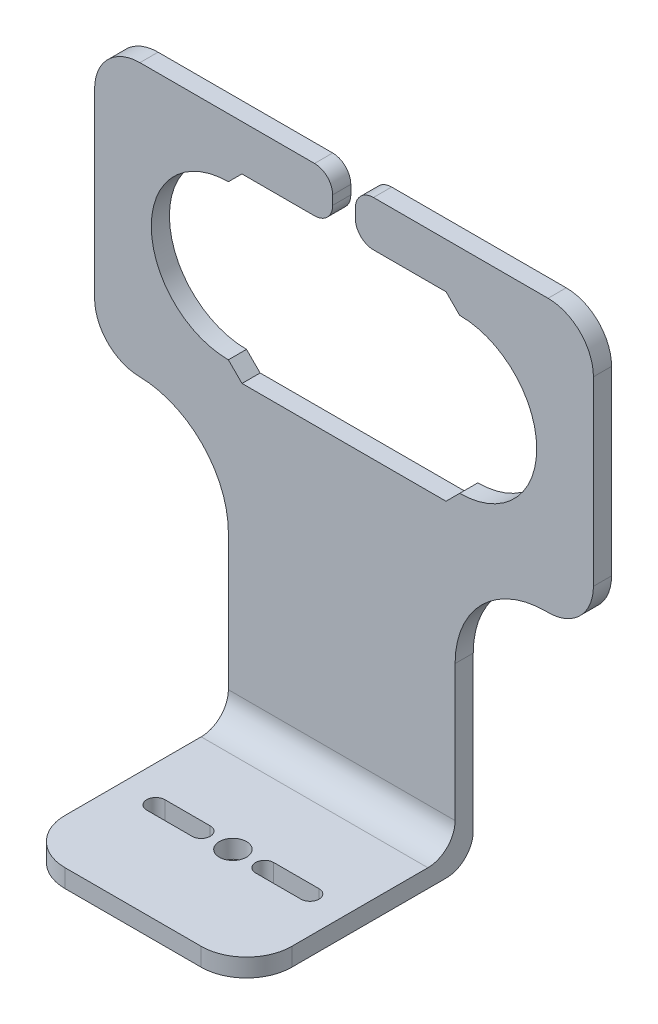
SolidWorks part; units mm, degrees
material "ABS"
ref_plane "Front Plane" through (0, 0, 0) normal (0, 0, 1) x (1, 0, 0)
ref_plane "Top Plane" through (0, 0, 0) normal (0, 1, 0) x (1, 0, 0)
ref_plane "Right Plane" through (0, 0, 0) normal (1, 0, 0) x (0, 0, -1)
sketch "Sketch1" plane through (0, 0, 0) normal (0, 0, 1) x (1, 0, 0)
  line L0 (-1.3335, 27.9084) -> (-1.3335, 26.9043)
  line L1 (-22.5835, 29.9084) -> (-3.3335, 29.9084)
  line L2 (-27.5835, 24.9084) -> (-27.5835, 4.9043)
  line L4 (27.4165, 24.9084) -> (27.4165, 4.9043)
  line L5 (-11.3376, 24.9043) -> (-3.3335, 24.9043)
  line L7 (-12.8335, -30.0916) -> (-12.8335, -0.0957)
  line L8 (12.1665, -30.0916) -> (12.1665, -0.0957)
  line L9 (-22.5835, -0.0957) -> (-12.8335, -0.0957)
  line L11 (12.1665, -0.0957) -> (22.4165, -0.0957)
  line L14 (-11.3294, 4.9043) -> (11.1624, 4.9043)
  line L16 (-12.8335, 23.4084) -> (-11.3376, 24.9043)
  line L17 (12.6665, 23.4084) -> (11.1706, 24.9043)
  line L18 (1.1665, 27.9084) -> (1.1665, 26.9043)
  line L19 (-12.8335, 6.4084) -> (-11.3294, 4.9043)
  line L20 (12.6665, 6.4084) -> (11.1624, 4.9043)
  line L21 (3.1665, 24.9043) -> (11.1706, 24.9043)
  line L22 (3.1665, 29.9084) -> (22.4165, 29.9084)
  line L23 (12.1665, -30.0916) -> (-12.8335, -30.0916)
  arc A0 (-12.8335, 23.4084) -> (-12.8335, 6.4084) centre (-12.8335, 14.9084) ccw
  arc A1 (12.6665, 6.4084) -> (12.6665, 23.4084) centre (12.6665, 14.9084) ccw
  arc A2 (22.4165, 29.9084) -> (27.4165, 24.9084) centre (22.4165, 24.9084) cw
  arc A3 (27.4165, 4.9043) -> (22.4165, -0.0957) centre (22.4165, 4.9043) cw
  arc A4 (-22.5835, -0.0957) -> (-27.5835, 4.9043) centre (-22.5835, 4.9043) cw
  arc A5 (-22.5835, 29.9084) -> (-27.5835, 24.9084) centre (-22.5835, 24.9084) ccw
  arc A6 (1.1665, 26.9043) -> (3.1665, 24.9043) centre (3.1665, 26.9043) ccw
  arc A7 (3.1665, 29.9084) -> (1.1665, 27.9084) centre (3.1665, 27.9084) ccw
  arc A8 (-3.3335, 29.9084) -> (-1.3335, 27.9084) centre (-3.3335, 27.9084) cw
  arc A9 (-1.3335, 26.9043) -> (-3.3335, 24.9043) centre (-3.3335, 26.9043) cw
  point P0 (0, 0)
  point P39 (1.1665, 24.9043)
  dimension "D4" = 15
  dimension "D5" = 26.25
  dimension "D10" = 60
  dimension "D9" = 2
  dimension "D8" = 5
  dimension "D1" = 15
  dimension "D2" = 14.75
  dimension "D3" = 14.75
  dimension "D6" = 2.5
  dimension "D7" = 25
extrude "Boss-Extrude1" add sketch "Sketch1" against normal blind 2
sketch "Sketch2" plane through (0, 0, 0) normal (0, 0, 1) x (1, 0, 0)
  line L0 (12.1665, -30.0916) -> (12.1665, -0.0957) construction
  line L1 (-12.8335, -30.0916) -> (12.1665, -30.0916)
  line L2 (-12.8335, -30.0916) -> (-12.8335, -28.0916)
  line L3 (-12.8335, -28.0916) -> (12.1665, -28.0916)
  line L4 (12.1665, -30.0916) -> (12.1665, -28.0916)
  dimension "D1" = 2
extrude "Boss-Extrude2" add sketch "Sketch2" along normal blind 23
fillet "Fillet1" radius 3 2 edges at (-0.3335, -28.0916, 0) (-0.3335, -30.0916, -2)
fillet "Fillet2" radius 10 2 edges at (-12.8335, -0.0957, -1) (12.1665, -0.0957, -1)
fillet "Fillet3" radius 5 2 edges at (12.1665, -29.0916, 23) (-12.8335, -29.0916, 23)
sketch "Sketch3" plane through (0, -30.0916, 0) normal (0, -1, 0) x (1, 0, 0)
  line L0 (-20.4571, 12) -> (18.6063, 12) construction
  line L1 (-22.6668, -2) -> (-12.8335, -2) construction
  line L2 (-0.3335, 25.8555) -> (-0.3335, -3.8911) construction
  line L3 (-12.8335, 1) -> (-12.8335, 18) construction
  line L5 (3.1665, 12) -> (8.1665, 12) construction
  line L6 (3.1665, 13) -> (8.1665, 13)
  line L7 (3.1665, 11) -> (8.1665, 11)
  line L8 (-3.8335, 12) -> (-8.8335, 12) construction
  line L9 (-3.8335, 11) -> (-8.8335, 11)
  line L10 (-3.8335, 13) -> (-8.8335, 13)
  circle A0 centre (-0.3335, 12) radius 1.5
  arc A1 (3.1665, 13) -> (3.1665, 11) centre (3.1665, 12) ccw
  arc A2 (8.1665, 11) -> (8.1665, 13) centre (8.1665, 12) ccw
  arc A3 (-3.8335, 11) -> (-3.8335, 13) centre (-3.8335, 12) ccw
  arc A4 (-8.8335, 13) -> (-8.8335, 11) centre (-8.8335, 12) ccw
  point P12 (5.6665, 12)
  point P19 (-6.3335, 12)
  dimension "D3" = 3.5
  dimension "D4" = 3.5
  dimension "D1" = 14
  dimension "D2" = 12.5
extrude "Cut-Extrude1" cut sketch "Sketch3" against normal up to surface (2 mm away) contours A0 | L7 A2 L6 A1 | L10 A4 L9 A3 up to face at (-0.3335, -28.0916, 15.0118)
